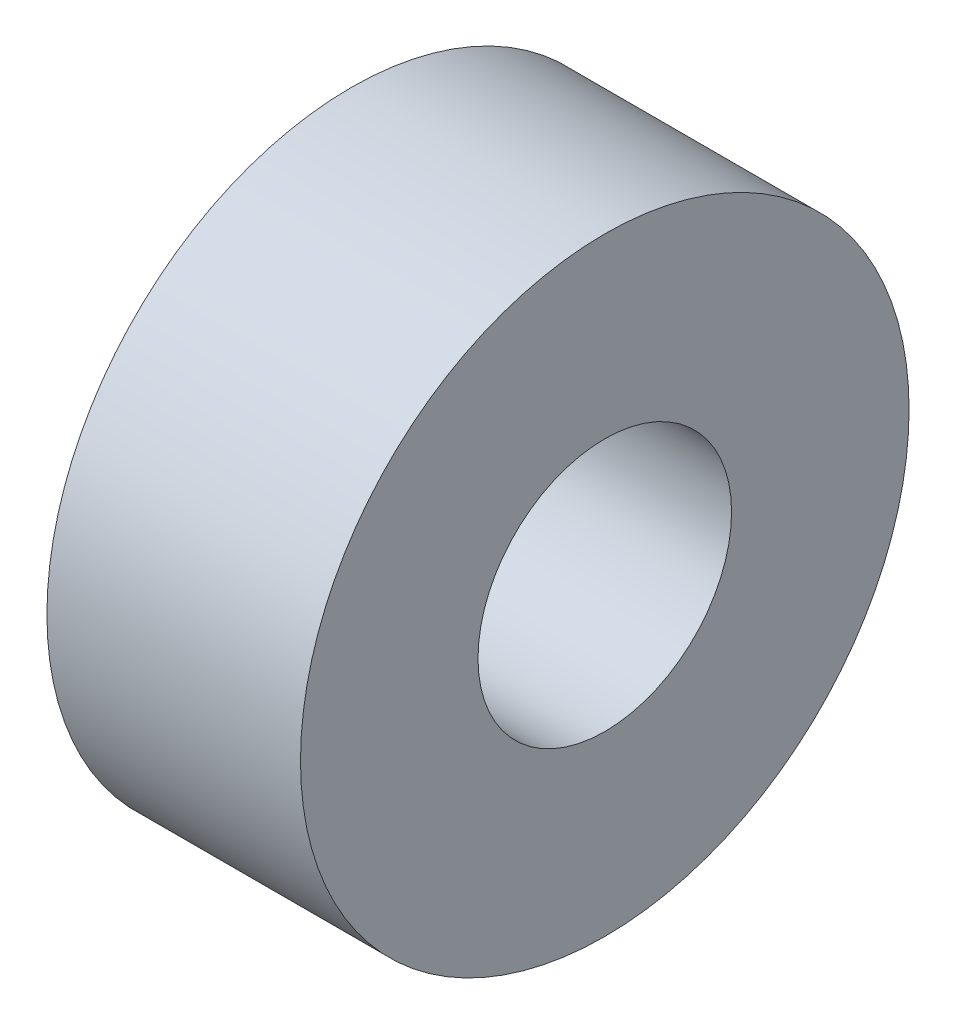
SolidWorks part; units mm, degrees
ref_plane "前视基准面" through (0, 0, 0) normal (0, 0, 1) x (1, 0, 0)
ref_plane "上视基准面" through (0, 0, 0) normal (0, 1, 0) x (1, 0, 0)
ref_plane "右视基准面" through (0, 0, 0) normal (1, 0, 0) x (0, 0, -1)
sketch "草图1" plane through (0, 0, 0) normal (1, 0, 0) x (0, 0, -1)
  circle A0 centre (0, 0) radius 2.5
  circle A1 centre (0, 0) radius 6
  dimension "D1" = 5
  dimension "D2" = 12
extrude "凸台-拉伸1" add sketch "草图1" along normal blind 5
